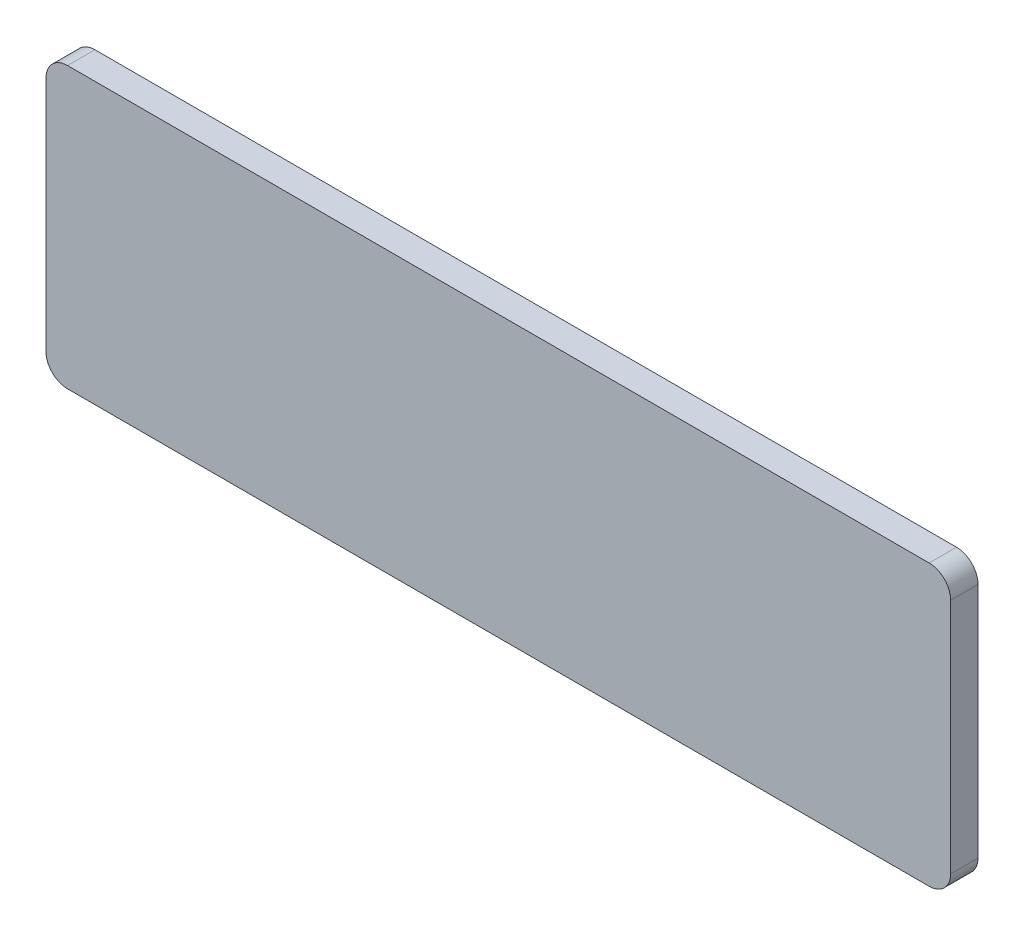
SolidWorks part; units mm, degrees
material "Pine"
ref_plane "Front Plane" through (0, 0, 0) normal (0, 0, 1) x (1, 0, 0)
ref_plane "Top Plane" through (0, 0, 0) normal (0, 1, 0) x (1, 0, 0)
ref_plane "Right Plane" through (0, 0, 0) normal (1, 0, 0) x (0, 0, -1)
sketch "Sketch1" plane through (0, 0, 0) normal (0, 0, 1) x (1, 0, 0)
  line L0 (-105, 32.5) -> (105, 32.5)
  line L1 (-105, 32.5) -> (-105, -32.5)
  line L2 (105, 32.5) -> (105, -32.5)
  line L3 (-105, -32.5) -> (105, -32.5)
  line L4 (105, -32.5) -> (-105, 32.5) construction
  point P0 (0, 0)
  point P7 (-102.0991, 33.1409)
  dimension "D1" = 65
  dimension "D2" = 210
extrude "Boss-Extrude1" add sketch "Sketch1" along normal mid plane 6.35
fillet "Fillet1" radius 5 4 edges at (-105, -32.5, 0) (-105, 32.5, 0) (105, -32.5, 0) (105, 32.5, 0)
